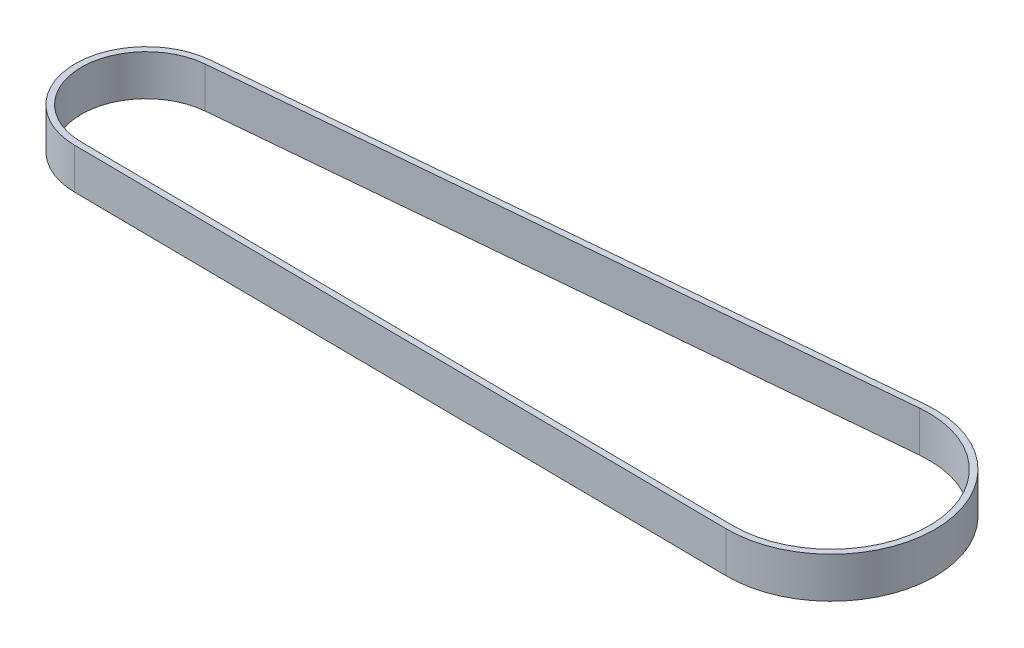
SolidWorks part; units mm, degrees
material "BUTYL"
ref_plane "Front Plane" through (0, 0, 0) normal (0, 0, 1) x (1, 0, 0)
ref_plane "Top Plane" through (0, 0, 0) normal (0, 1, 0) x (1, 0, 0)
ref_plane "Right Plane" through (0, 0, 0) normal (1, 0, 0) x (0, 0, -1)
sketch "Sketch1" plane through (0, 0, 0) normal (0, 1, 0) x (1, 0, 0)
  line L0 (-72.7542, 9.354) -> (88.109, 23.9024)
  line L1 (-71.4772, -22.4106) -> (90.0348, -23.9988)
  line L2 (-72.8893, 10.8479) -> (87.9739, 25.3963)
  line L3 (-71.4919, -23.9105) -> (90.02, -25.4988)
  arc A0 (-72.7542, 9.354) -> (-71.4772, -22.4106) centre (-71.3207, -6.4963) ccw
  arc A1 (90.0348, -23.9988) -> (88.109, 23.9024) centre (90.2708, 0) ccw
  arc A2 (90.02, -25.4988) -> (87.9739, 25.3963) centre (90.2708, 0) ccw
  arc A3 (-72.8893, 10.8479) -> (-71.4919, -23.9105) centre (-71.3207, -6.4963) ccw
  dimension "D2" = 31.83
  dimension "D3" = 48
  dimension "D1" = 161.722
  dimension "D4" = 1.5
extrude "Boss-Extrude1" add sketch "Sketch1" along normal blind 10
